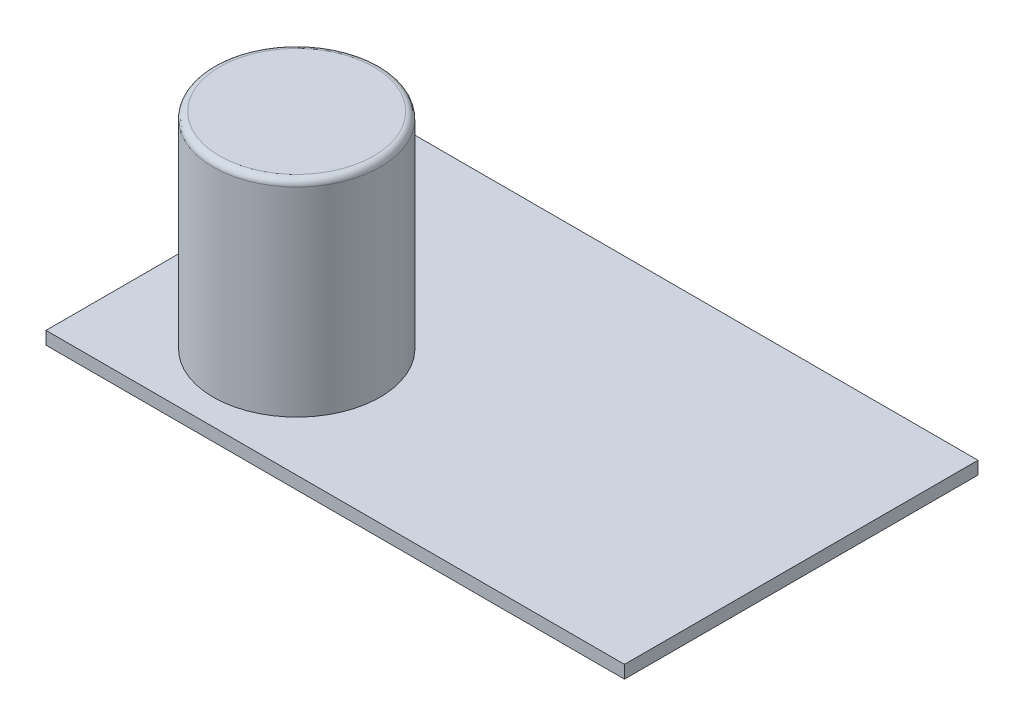
SolidWorks part; units mm, degrees
ref_plane "Спереди" through (0, 0, 0) normal (0, 0, 1) x (1, 0, 0)
ref_plane "Сверху" through (0, 0, 0) normal (0, 1, 0) x (1, 0, 0)
ref_plane "Справа" through (0, 0, 0) normal (1, 0, 0) x (0, 0, -1)
sketch "Эскиз1" plane through (0, 0, 0) normal (0, 1, 0) x (1, 0, 0)
  line L1 (0, 0) -> (45, 0)
  line L2 (0, 0) -> (0, 27.5)
  line L3 (0, 27.5) -> (45, 27.5)
  line L4 (45, 0) -> (45, 27.5)
  dimension "D1" = 27.5
  dimension "D2" = 45
extrude "Бобышка-Вытянуть1" add sketch "Эскиз1" along normal blind 1
sketch "Эскиз2" plane through (0, 1, 0) normal (0, 1, 0) x (1, 0, 0)
  line L1 (0, 27.5) -> (0, 0) construction
  line L2 (0, 0) -> (45, 0) construction
  circle A0 centre (11, 8.5) radius 6.5
  point P2 (4.5, 8.5)
  point P3 (11, 2)
  dimension "D1" = 13
  dimension "D2" = 4.5
  dimension "D3" = 2
extrude "Бобышка-Вытянуть2" add sketch "Эскиз2" along normal blind 16 separate body
fillet "Скругление1" radius 0.5 1 edges at (11, 17, -2)
